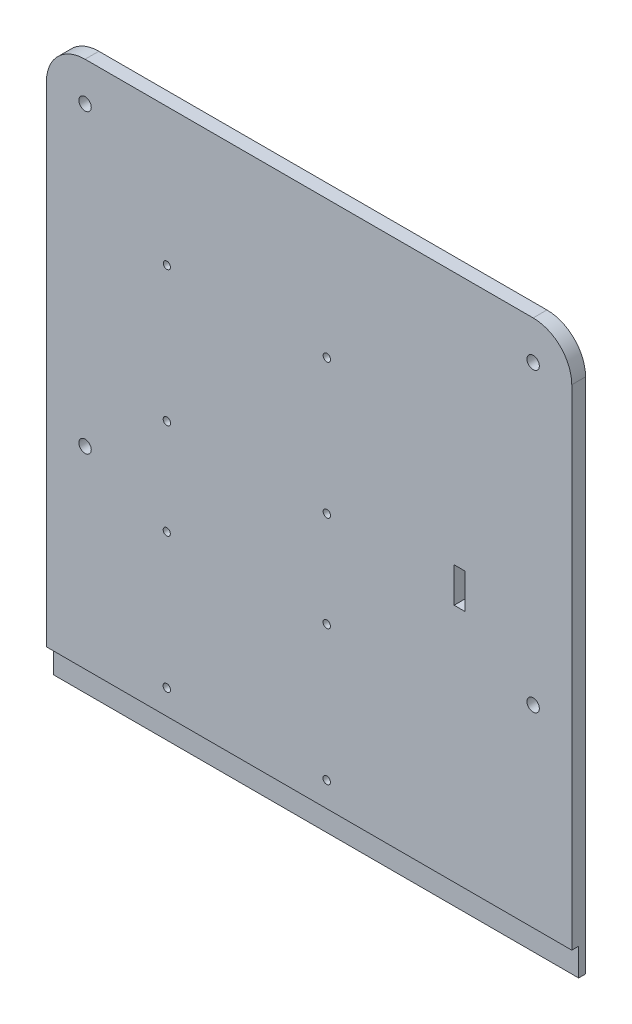
SolidWorks part; units mm, degrees
ref_plane "Front Plane" through (0, 0, 0) normal (0, 0, 1) x (1, 0, 0)
ref_plane "Top Plane" through (0, 0, 0) normal (0, 1, 0) x (1, 0, 0)
ref_plane "Right Plane" through (0, 0, 0) normal (1, 0, 0) x (0, 0, -1)
sketch "Sketch4" plane through (0, 0, 0) normal (0, 0, 1) x (1, 0, 0)
  line L0 (-66.0801, -1201.5626) -> (96.4199, -1201.5626)
  line L1 (-80.0801, -1187.5626) -> (-80.0801, -812.4374)
  line L2 (96.4199, -798.4374) -> (-66.0801, -798.4374)
  line L3 (110.4199, -812.4374) -> (110.4199, -1187.5626)
  circle A0 centre (96.4199, -1187.5626) radius 2.25
  circle A1 centre (-66.0801, -1187.5626) radius 2.25
  circle A2 centre (-66.0801, -1080) radius 2.25
  circle A3 centre (-66.0801, -920) radius 2.25
  circle A4 centre (-66.0801, -812.4374) radius 2.25
  circle A5 centre (96.4199, -812.4374) radius 2.25
  circle A6 centre (96.4199, -920) radius 2.25
  circle A7 centre (96.4199, -1080) radius 2.25
  circle A8 centre (96.4199, -1080) radius 14
  circle A9 centre (96.4199, -1187.5626) radius 14
  circle A10 centre (-66.0801, -1187.5626) radius 14
  circle A11 centre (-66.0801, -1080) radius 14
  circle A12 centre (-66.0801, -920) radius 14
  circle A13 centre (88.1478, -1029.08) radius 7.9375
  circle A14 centre (96.4199, -920) radius 14
  circle A15 centre (96.4199, -812.4374) radius 14
  circle A16 centre (-66.0801, -812.4374) radius 14
  point P0 (96.4199, -1182.7361)
  point P1 (96.4199, -1080)
  point P3 (96.4199, -920)
  point P5 (96.4199, -812.4374)
  point P7 (-66.0801, -812.4374)
  point P9 (-66.0801, -920)
  point P11 (-66.0801, -1080)
  point P13 (-66.0801, -1187.5626)
  dimension "D1" = 28
extrude "Boss-Extrude1" add sketch "Sketch4" along normal blind 5
sketch "Sketch5" plane through (110.4199, 0, 0) normal (1, 0, 0) x (0, 0, -1)
  line L0 (0, -1000) -> (-5, -1000) construction
  line L1 (0, -812.4374) -> (0, -1187.5626) construction
  line L2 (-5, -812.4374) -> (-5, -1187.5626) construction
  line L3 (-2.5, -1000) -> (-2.5, -990) construction
  line L4 (-2.5, -990) -> (-5, -990) construction
  line L5 (-5, -990) -> (-107.6346, -1208.9532) construction
  line L6 (-107.6346, -1208.9532) -> (44.9904, -1241.1394) construction
  line L7 (44.9904, -1241.1394) -> (57.2004, -1033.1682) construction
  line L8 (-2.5, -990) -> (-2.5, -1000)
  line L9 (-2.5, -1000) -> (0, -1000)
  line L10 (0, -1000) -> (105.3301, -1133.4852)
  line L11 (105.3301, -1133.4852) -> (-31.1004, -1241.1394)
  line L12 (-31.1004, -1241.1394) -> (-117.7847, -1052.2967)
  line L13 (-117.7847, -1052.2967) -> (-5, -990)
  line L14 (-5, -990) -> (-2.5, -990)
  dimension "D1" = 10
extrude "Cut-Extrude1" cut sketch "Sketch5" against normal through all
sketch "Sketch6" plane through (0, 0, 5) normal (0, 0, 1) x (1, 0, 0)
  line L0 (96.4199, -798.4374) -> (-66.0801, -798.4374) construction
  line L1 (-61.0801, -838.4374) -> (91.4199, -838.4374)
  line L2 (-61.0801, -838.4374) -> (-61.0801, -1024.81)
  line L3 (-61.0801, -1024.81) -> (91.4199, -1024.81)
  line L4 (91.4199, -838.4374) -> (91.4199, -1024.81)
  line L5 (110.4199, -812.4374) -> (110.4199, -990) construction
  line L6 (-80.0801, -990) -> (-80.0801, -812.4374) construction
  line L7 (21.593, -846.5006) -> (79.593, -846.5006)
  line L8 (-37.9102, -926.6548) -> (20.0898, -926.6548)
  line L9 (-37.9102, -926.6548) -> (-37.9102, -975.6548)
  line L10 (-37.9102, -975.6548) -> (20.0898, -975.6548)
  line L11 (20.0898, -926.6548) -> (20.0898, -975.6548)
  line L12 (21.593, -846.5006) -> (21.593, -895.5006)
  line L13 (21.593, -895.5006) -> (79.593, -895.5006)
  line L14 (79.593, -846.5006) -> (79.593, -895.5006)
  circle A0 centre (20.0898, -926.6548) radius 1.3
  circle A1 centre (20.0898, -975.6548) radius 1.3
  circle A2 centre (-37.9102, -926.6548) radius 1.3
  circle A3 centre (-37.9102, -975.6548) radius 1.3
  dimension "D4" = 2.6
  dimension "D1" = 40
  dimension "D2" = 19
  dimension "D3" = 19
  dimension "D5" = 49
  dimension "D6" = 58
sketch "Sketch7" plane through (0, 0, 0) normal (0, 0, -1) x (1, 0, 0)
  line L0 (-80.0801, 1000) -> (110.4199, 1000) construction
  line L1 (110.4199, 812.4374) -> (110.4199, 1000) construction
  line L4 (81.9199, 852.4374) -> (91.4199, 852.4374)
  line L5 (77.4199, 838.4374) -> (77.4199, 847.9374)
  line L6 (91.4199, 852.4374) -> (91.4199, 901.6697)
  line L7 (77.4199, 920) -> (77.4199, 944.5357)
  line L8 (81.9199, 949.0357) -> (91.4199, 949.0357)
  line L9 (91.4199, 949.0357) -> (91.4199, 990)
  line L10 (-61.0801, 1000) -> (-61.0801, 949.0357)
  line L11 (-61.0801, 949.0357) -> (-51.5801, 949.0357)
  line L12 (-47.0801, 944.5357) -> (-47.0801, 920)
  line L13 (-61.0801, 901.6697) -> (-61.0801, 852.4374)
  line L14 (-61.0801, 852.4374) -> (-51.5801, 852.4374)
  line L15 (-47.0801, 847.9374) -> (-47.0801, 838.4374)
  line L16 (-47.0801, 838.4374) -> (77.4199, 838.4374)
  arc A0 (81.9199, 852.4374) -> (77.4199, 847.9374) centre (81.9199, 847.9374) ccw
  arc A1 (77.4199, 920) -> (91.4199, 901.6697) centre (96.4199, 920) ccw
  arc A2 (81.9199, 949.0357) -> (77.4199, 944.5357) centre (81.9199, 944.5357) ccw
  arc A3 (-47.0801, 944.5357) -> (-51.5801, 949.0357) centre (-51.5801, 944.5357) ccw
  arc A4 (-61.0801, 901.6697) -> (-47.0801, 920) centre (-66.0801, 920) ccw
  arc A5 (-47.0801, 847.9374) -> (-51.5801, 852.4374) centre (-51.5801, 847.9374) ccw
  dimension "D1" = 10
  dimension "D2" = 19
sketch "Sketch8" plane through (0, 0, 0) normal (0, 0, -1) x (1, 0, 0)
  line L0 (21.5947, 848.3067) -> (-36.4053, 848.3067) construction
  line L1 (-36.4053, 848.3067) -> (-36.4053, 897.3067) construction
  line L2 (-36.4053, 897.3067) -> (21.5947, 897.3067) construction
  line L3 (21.5947, 897.3067) -> (21.5947, 848.3067) construction
  line L4 (50.5761, 843.566) -> (50.5761, 903.315) construction
  line L5 (50.5761, 903.315) -> (-42.8627, 903.315) construction
  line L6 (-42.8627, 903.315) -> (-42.8627, 843.566) construction
  line L7 (-42.8627, 843.566) -> (50.5761, 843.566) construction
  line L8 (-42.8627, 897.9995) -> (50.5761, 897.9995) construction
  line L9 (45.6952, 903.315) -> (45.6952, 843.566) construction
  circle A0 centre (-36.4053, 897.3067) radius 1.35
  circle A1 centre (21.5947, 897.3067) radius 1.35
  circle A2 centre (21.5947, 848.3067) radius 1.35
  circle A3 centre (-36.4053, 848.3067) radius 1.3
sketch "Sketch9" plane through (0, 0, 0) normal (0, 0, -1) x (1, 0, 0)
  line L0 (21.5487, 932.0418) -> (-36.4513, 932.0418) construction
  line L1 (-36.4513, 932.0418) -> (-36.4513, 981.0418) construction
  line L2 (-36.4513, 981.0418) -> (21.5487, 981.0418) construction
  line L3 (21.5487, 981.0418) -> (21.5487, 932.0418) construction
  line L4 (50.5301, 927.301) -> (50.5301, 987.0501) construction
  line L5 (50.5301, 987.0501) -> (-42.9087, 987.0501) construction
  line L6 (-42.9087, 987.0501) -> (-42.9087, 927.301) construction
  line L7 (-42.9087, 927.301) -> (50.5301, 927.301) construction
  line L8 (-42.9087, 981.7346) -> (50.5301, 981.7346) construction
  line L9 (45.6492, 987.0501) -> (45.6492, 927.301) construction
  circle A0 centre (-36.4513, 981.0418) radius 1.35
  circle A1 centre (21.5487, 981.0418) radius 1.35
  circle A2 centre (21.5487, 932.0418) radius 1.35
  circle A3 centre (-36.4513, 932.0418) radius 1.3
extrude "Cut-Extrude2" cut sketch "Sketch8" against normal through all
extrude "Cut-Extrude3" cut sketch "Sketch9" against normal through all
sketch "Sketch11" plane through (0, 0, 0) normal (0, 0, -1) x (-1, 0, 0)
  line L1 (-20.1225, -845.7567) -> (-23.067, -845.7567)
  line L2 (-23.067, -845.7567) -> (-24.5392, -848.3067)
  line L3 (-24.5392, -848.3067) -> (-23.067, -850.8567)
  line L4 (-23.067, -850.8567) -> (-20.1225, -850.8567)
  line L5 (-20.1225, -850.8567) -> (-18.6502, -848.3067)
  line L6 (-18.6502, -848.3067) -> (-20.1225, -845.7567)
  line L7 (34.933, -845.7567) -> (33.4608, -848.3067)
  line L8 (33.4608, -848.3067) -> (34.933, -850.8567)
  line L9 (34.933, -850.8567) -> (37.8775, -850.8567)
  line L10 (37.8775, -850.8567) -> (39.3498, -848.3067)
  line L11 (39.3498, -848.3067) -> (37.8775, -845.7567)
  line L12 (37.8775, -845.7567) -> (34.933, -845.7567)
  line L13 (34.933, -894.7567) -> (33.4608, -897.3067)
  line L14 (33.4608, -897.3067) -> (34.933, -899.8567)
  line L15 (34.933, -899.8567) -> (37.8775, -899.8567)
  line L16 (37.8775, -899.8567) -> (39.3498, -897.3067)
  line L17 (39.3498, -897.3067) -> (37.8775, -894.7567)
  line L18 (37.8775, -894.7567) -> (34.933, -894.7567)
  line L19 (-20.1225, -894.7567) -> (-23.067, -894.7567)
  line L20 (-23.067, -894.7567) -> (-24.5392, -897.3067)
  line L21 (-24.5392, -897.3067) -> (-23.067, -899.8567)
  line L22 (-23.067, -899.8567) -> (-20.1225, -899.8567)
  line L23 (-20.1225, -899.8567) -> (-18.6502, -897.3067)
  line L24 (-18.6502, -897.3067) -> (-20.1225, -894.7567)
  line L25 (-20.0765, -929.4918) -> (-23.021, -929.4918)
  line L26 (-23.021, -929.4918) -> (-24.4932, -932.0418)
  line L27 (-24.4932, -932.0418) -> (-23.021, -934.5918)
  line L28 (-23.021, -934.5918) -> (-20.0765, -934.5918)
  line L29 (-20.0765, -934.5918) -> (-18.6042, -932.0418)
  line L30 (-18.6042, -932.0418) -> (-20.0765, -929.4918)
  line L31 (34.979, -929.4918) -> (33.5068, -932.0418)
  line L32 (33.5068, -932.0418) -> (34.979, -934.5918)
  line L33 (34.979, -934.5918) -> (37.9235, -934.5918)
  line L34 (37.9235, -934.5918) -> (39.3958, -932.0418)
  line L35 (39.3958, -932.0418) -> (37.9235, -929.4918)
  line L36 (37.9235, -929.4918) -> (34.979, -929.4918)
  line L37 (-23.021, -978.4918) -> (-24.4932, -981.0418)
  line L38 (-24.4932, -981.0418) -> (-23.021, -983.5918)
  line L39 (-23.021, -983.5918) -> (-20.0765, -983.5918)
  line L40 (-20.0765, -983.5918) -> (-18.6042, -981.0418)
  line L41 (-18.6042, -981.0418) -> (-20.0765, -978.4918)
  line L42 (-20.0765, -978.4918) -> (-23.021, -978.4918)
  line L43 (34.979, -978.4918) -> (33.5068, -981.0418)
  line L44 (33.5068, -981.0418) -> (34.979, -983.5918)
  line L45 (34.979, -983.5918) -> (37.9235, -983.5918)
  line L46 (37.9235, -983.5918) -> (39.3958, -981.0418)
  line L47 (39.3958, -981.0418) -> (37.9235, -978.4918)
  line L48 (37.9235, -978.4918) -> (34.979, -978.4918)
  circle A0 centre (-21.5947, -848.3067) radius 2.55 construction
  circle A1 centre (36.4053, -848.3067) radius 2.55 construction
  circle A2 centre (36.4053, -897.3067) radius 2.55 construction
  circle A3 centre (-21.5947, -897.3067) radius 2.55 construction
  circle A4 centre (-21.5487, -932.0418) radius 2.55 construction
  circle A5 centre (36.4513, -932.0418) radius 2.55 construction
  circle A6 centre (-21.5487, -981.0418) radius 2.55 construction
  circle A7 centre (36.4513, -981.0418) radius 2.55 construction
  dimension "D1" = 5.1
  dimension "5.1" = 5.1
  dimension "D3" = 5.1
  dimension "D4" = 5.1
  dimension "D5" = 5.1
  dimension "D6" = 5.1
  dimension "D7" = 5.1
  dimension "D8" = 5.1
extrude "Cut-Extrude4" cut sketch "Sketch11" against normal blind 2.4
sketch "Sketch12" plane through (0, 0, 5) normal (0, 0, 1) x (1, 0, 0)
  line L1 (67.7593, -890.3014) -> (71.7593, -890.3014)
  line L2 (67.7593, -890.3014) -> (67.7593, -903.0014)
  line L3 (67.7593, -903.0014) -> (71.7593, -903.0014)
  line L4 (71.7593, -890.3014) -> (71.7593, -903.0014)
  dimension "D1" = 12.7
  dimension "D2" = 4
extrude "Cut-Extrude5" cut sketch "Sketch12" against normal through all
